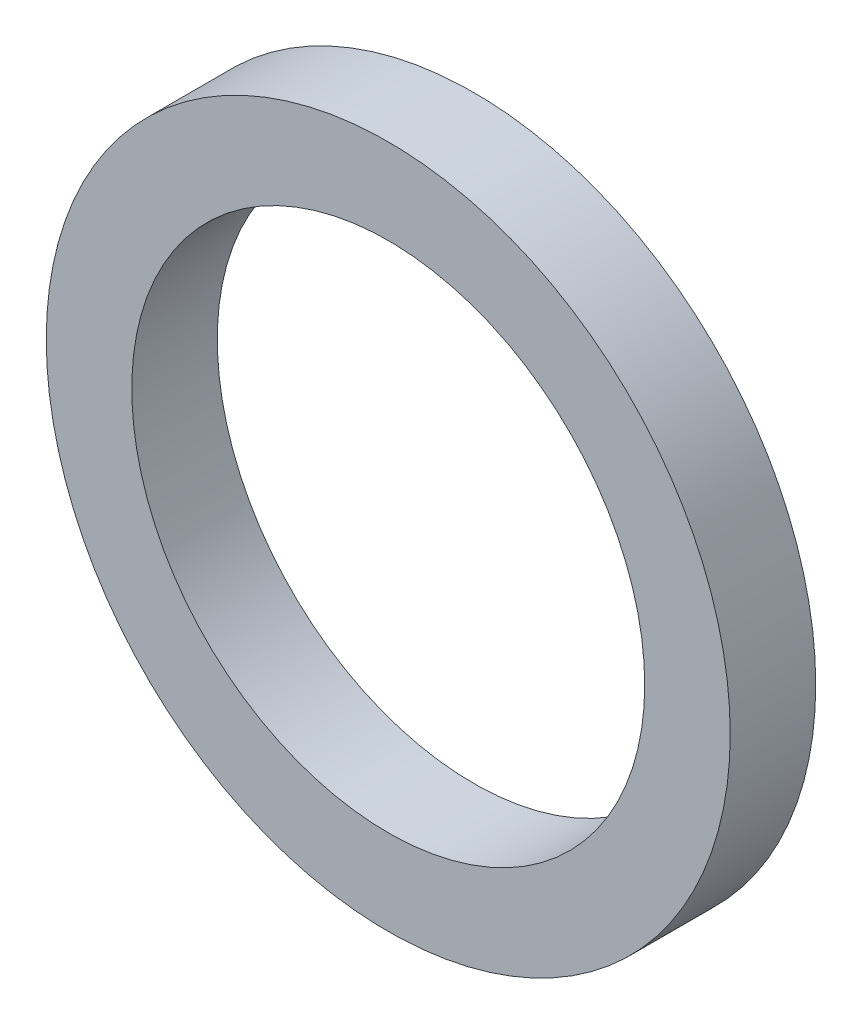
SolidWorks part; units mm, degrees
ref_plane "Alzado" through (0, 0, 0) normal (0, 0, 1) x (1, 0, 0)
ref_plane "Planta" through (0, 0, 0) normal (0, 1, 0) x (1, 0, 0)
ref_plane "Vista lateral" through (0, 0, 0) normal (1, 0, 0) x (0, 0, -1)
sketch "Croquis1" plane through (0, 0, 0) normal (0, 0, 1) x (1, 0, 0)
  circle A0 centre (0, 0) radius 3
  circle A1 centre (0, 0) radius 4
  dimension "D1" = 6
  dimension "D2" = 8
extrude "Saliente-Extruir1" add sketch "Croquis1" along normal blind 1
